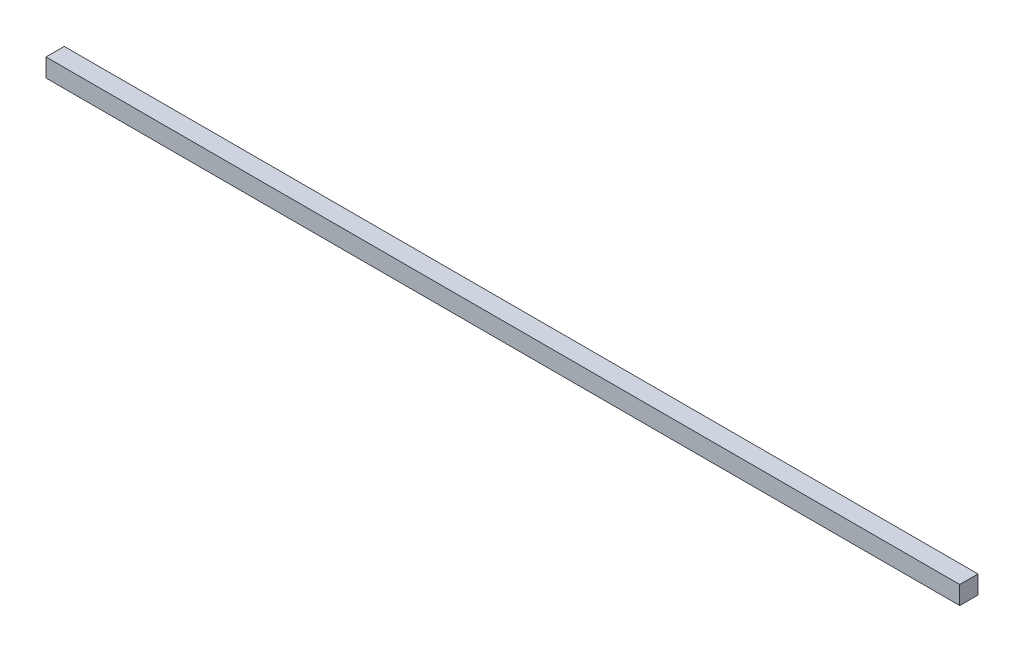
SolidWorks part; units mm, degrees
ref_plane "Front Plane" through (0, 0, 0) normal (0, 0, 1) x (1, 0, 0)
ref_plane "Top Plane" through (0, 0, 0) normal (0, 1, 0) x (1, 0, 0)
ref_plane "Right Plane" through (0, 0, 0) normal (1, 0, 0) x (0, 0, -1)
sketch "Sketch1" plane through (0, 0, 0) normal (1, 0, 0) x (0, 0, -1)
  line L1 (-1, -1) -> (1, -1)
  line L2 (-1, -1) -> (-1, 1)
  line L3 (-1, 1) -> (1, 1)
  line L4 (1, -1) -> (1, 1)
  line L5 (-1, -1) -> (1, 1) construction
  line L6 (-1, 1) -> (1, -1) construction
  point P0 (0, 0)
extrude "Boss-Extrude1" add sketch "Sketch1" along normal blind 100
